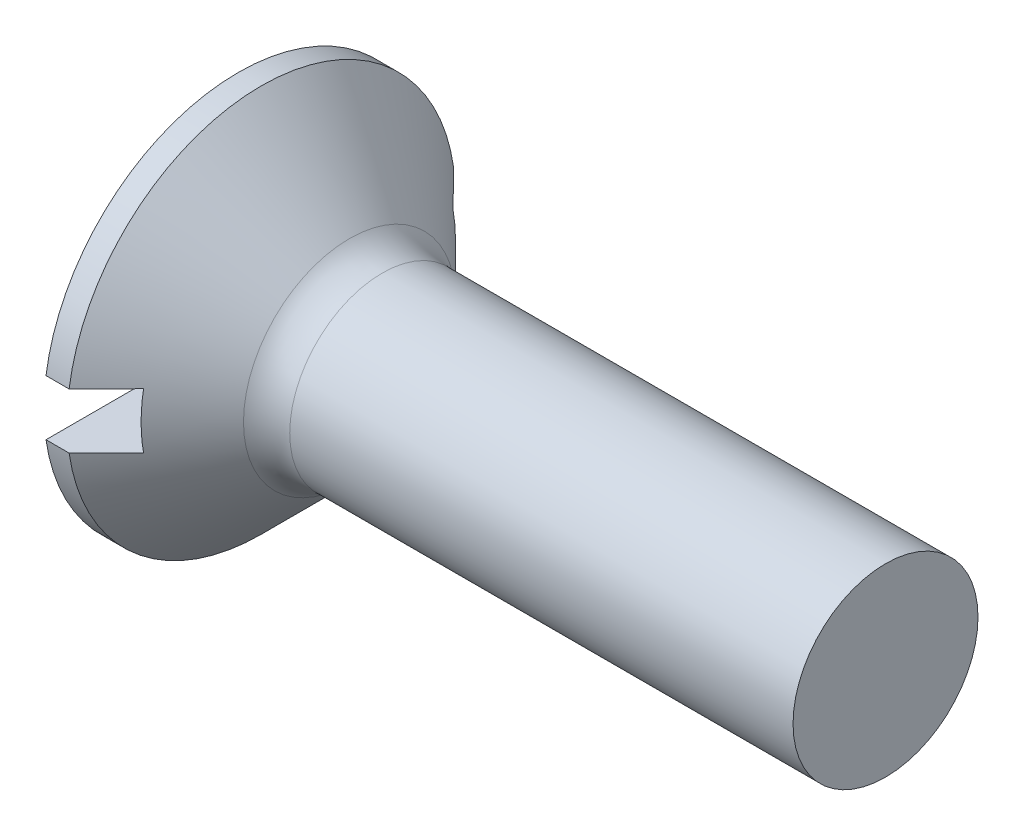
SolidWorks part; units mm, degrees
ref_plane "Plane1" through (0, 0, 0) normal (0, 0, 1) x (1, 0, 0)
ref_plane "Plane2" through (0, 0, 0) normal (0, 1, 0) x (1, 0, 0)
ref_plane "Plane3" through (0, 0, 0) normal (1, 0, 0) x (0, 0, -1)
sketch "BodySke" plane through (0, 0, 0) normal (0, 0, 1) x (1, 0, 0)
  line L0 (0, 0) -> (0, 4.2)
  line L1 (0, 4.2) -> (0.5, 4.2)
  line L2 (2.7, 2) -> (14, 2)
  line L3 (14, 2) -> (14, 0)
  line L4 (14, 0) -> (0, 0)
  line L5 (-6.35, 0) -> (82.55, 0) construction
  line L6 (2.7, -2) -> (14, -2) construction
  line L7 (0.5, -4.2) -> (2.7, -2) construction
  line L8 (0.5, 4.2) -> (2.7, 2)
  line L9 (0, -4.2) -> (0.5, -4.2) construction
  line L10 (3.4, 3.5875) -> (3.4, -5.9375) construction
  line L11 (-2, 6.35) -> (-2, -3.175) construction
  dimension "Diameter" = 4
  dimension "Length" = 14
  dimension "Head_ht" = 2.7
  dimension "Head_dia" = 8.4
  dimension "Head_ang" = 90
  dimension "D6" = 0.5
  dimension "Advance" = 0.7
  dimension "Thread_nom" = 16
revolve "Base-Revolve" add sketch "BodySke" angle 360 about L5
cosmetic thread "ThreadCosmetic" parameters "Thread_length"=10.6, "Thread_minor"=3.22
fillet "Fillet1" radius 1 1 edges at (2.7, 0, 2)
sketch "Sketch2" plane through (0, 0, 0) normal (-1, 0, 0) x (0, 0, 1)
  line L0 (-4.2, -0.6) -> (4.2, -0.6)
  line L1 (-4.2, -0.6) -> (-4.2, 0.6)
  line L2 (4.2, 0.6) -> (-4.2, 0.6)
  line L3 (4.2, 0.6) -> (4.2, -0.6)
  dimension "D1" = 0.6
  dimension "Slot_width" = 1.2
  dimension "D2" = 8.4
  dimension "D3" = 4.2
extrude "Slot" cut sketch "Sketch2" against normal blind 1.3
sketch "ThdSchSke" plane through (0, 0, 0) normal (0, 0, 1) x (1, 0, 0)
  line L0 (3.4, -1.61) -> (3.1269, -2)
  line L1 (3.4, -1.61) -> (3.6731, -2)
  line L2 (3.6731, -2) -> (3.6731, -2.5)
  line L3 (-3.175, 0) -> (5.1513, 0) construction
  line L5 (3.6731, -2.5) -> (3.1269, -2.5)
  line L6 (3.1269, -2.5) -> (3.1269, -2)
  line L7 (0, 4.2) -> (0, 0.6) construction
  dimension "Thread_minor" = 3.22
  dimension "Diameter" = 4
  dimension "Start" = 3.4
  dimension "SideAngle" = 55
  dimension "VeeAngle" = 70
  dimension "Overcut" = 5
revolve "ThreadSchematic" [suppressed] cut sketch "ThdSchSke" angle 360 about L3
pattern_linear "ThdSchPat" [suppressed]
equation "\"D1@Sketch2\" = \"Slot_width@Sketch2\" / 2"
equation "\"D2@Sketch2\" = \"Head_dia@BodySke\""
equation "\"D3@Sketch2\" = \"D2@Sketch2\" / 2"
equation "\"Thread_length@ThreadCosmetic\" = ((sgn( (\"Length@BodySke\" - \"Advance@BodySke\" * 1.0 - \"Head_ht@BodySke\" ) - \"Thread_nom@BodySke\" )-1)*( (\"Length@BodySke\" - \"Advance@BodySke\" * 1.0 - \"Head_ht@BodySke\" ) - \"Thread_nom@BodySke\" ))/-2+ \"Thread_nom@BodySke\""
equation "\"Thread_minor@ThdSchSke\" = \"Thread_minor@ThreadCosmetic\""
equation "\"Diameter@ThdSchSke\" = \"Diameter@BodySke\""
equation "\"Overcut@ThdSchSke\" = \"Diameter@BodySke\" * 1.25"
equation "\"Start@ThdSchSke\" = 0.000001 + \"Length@BodySke\" - \"Thread_length@ThreadCosmetic\"  '---Countersunk---"
equation "\"Num_threads@ThdSchPat\" = int( \"Thread_length@ThreadCosmetic\" / \"Advance@BodySke\" + 0.999 )  + 1"
equation "\"Advance@ThdSchPat\" = \"Thread_length@ThreadCosmetic\" /  (\"Num_threads@ThdSchPat\" - 1) 'relax it"
